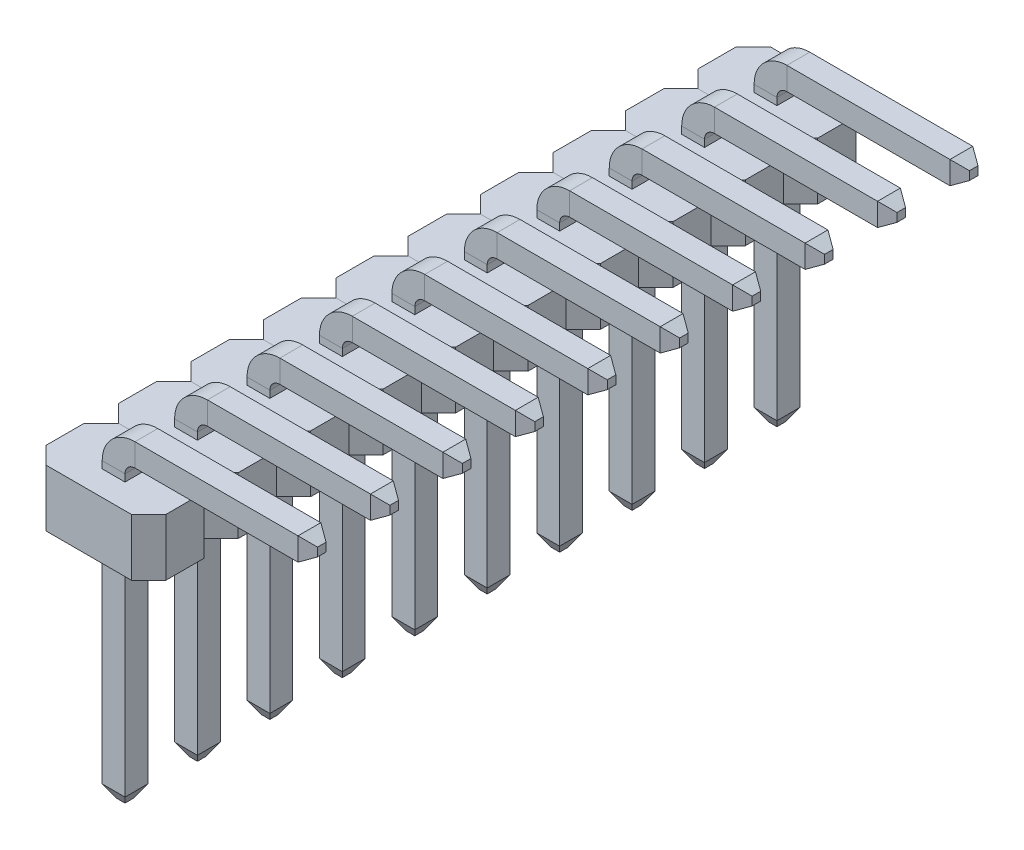
SolidWorks part; units mm, degrees
ref_plane "Front Plane" through (0, 0, 0) normal (0, 0, 1) x (1, 0, 0)
ref_plane "Top Plane" through (0, 0, 0) normal (0, 1, 0) x (1, 0, 0)
ref_plane "Right Plane" through (0, 0, 0) normal (1, 0, 0) x (0, 0, -1)
sketch "Sketch1" plane through (0, 0, 0) normal (0, 0, 1) x (1, 0, 0)
  line L0 (0.375, 0) -> (3.45, 0)
  line L1 (0, -0.375) -> (0, -5.5)
  line L2 (0, -1.5) -> (1.05, -1.5) construction
  arc A0 (0.375, 0) -> (0, -0.375) centre (0.375, -0.375) ccw
  point P8 (0, 0)
  dimension "D3" = 0.375
  dimension "D1" = 3.45
  dimension "D2" = 5.5
  dimension "D4" = 1.05
  dimension "D5" = 1.5
ref_plane "Plane1" through (0, -5.5, 0) normal (0, 1, 0) x (1, 0, 0)
sketch "Sketch2" plane through (0, -5.5, 0) normal (0, 1, 0) x (1, 0, 0)
  line L1 (-0.2, 0.2) -> (0.2, 0.2)
  line L2 (-0.2, 0.2) -> (-0.2, -0.2)
  line L3 (-0.2, -0.2) -> (0.2, -0.2)
  line L4 (0.2, 0.2) -> (0.2, -0.2)
  line L5 (-0.2, 0.2) -> (0.2, -0.2) construction
  line L6 (-0.2, -0.2) -> (0.2, 0.2) construction
  point P0 (0, 0)
  dimension "D1" = 0.4
sweep "Sweep1" add profiles "Sketch2" path "Sketch1"
chamfer "Chamfer1" distance 0.125 angle 60 4 edges at (0, -5.5, -0.2) (-0.2, -5.5, 0) (0, -5.5, 0.2) (0.2, -5.5, 0)
chamfer "Chamfer2" distance 0.125 angle 60 4 edges at (3.45, 0, 0.2) (3.45, 0.2, 0) (3.45, 0, -0.2) (3.45, -0.2, 0)
ref_plane "Plane2" through (0, -1.5, 0) normal (0, 1, 0) x (1, 0, 0)
sketch "Sketch3" plane through (0, -1.5, 0) normal (0, 1, 0) x (1, 0, 0)
  line L0 (-1.05, 0.335) -> (-0.75, 0.635)
  line L1 (-1.05, 0.635) -> (1.05, 0.635)
  line L2 (-1.05, 0.635) -> (-1.05, -0.635)
  line L3 (-1.05, -0.635) -> (1.05, -0.635)
  line L4 (1.05, 0.635) -> (1.05, -0.635)
  line L5 (-1.05, 0.635) -> (1.05, -0.635) construction
  line L6 (-1.05, -0.635) -> (1.05, 0.635) construction
  line L7 (-1.05, 0) -> (1.05, 0) construction
  line L8 (0, 0.635) -> (0, -0.635) construction
  line L9 (-1.05, -0.335) -> (-0.75, -0.635)
  line L10 (1.05, -0.335) -> (0.75, -0.635)
  line L11 (1.05, 0.335) -> (0.75, 0.635)
  point P0 (0, 0)
  point P19 (0, 0)
  dimension "D1" = 1.27
  dimension "D2" = 0.3
  dimension "D3" = 45
extrude "Boss-Extrude1" add sketch "Sketch3" along normal blind 1 contours L4 L11 L1 L0 L2 L9 L3 L10
pattern_linear "LPattern1" count 10 spacing 1.27 along (0, 0, 1) of bodies 102
ref_plane "Plane3" through (0, 0, 5.715) normal (0, 0, -1) x (-1, 0, 0)
